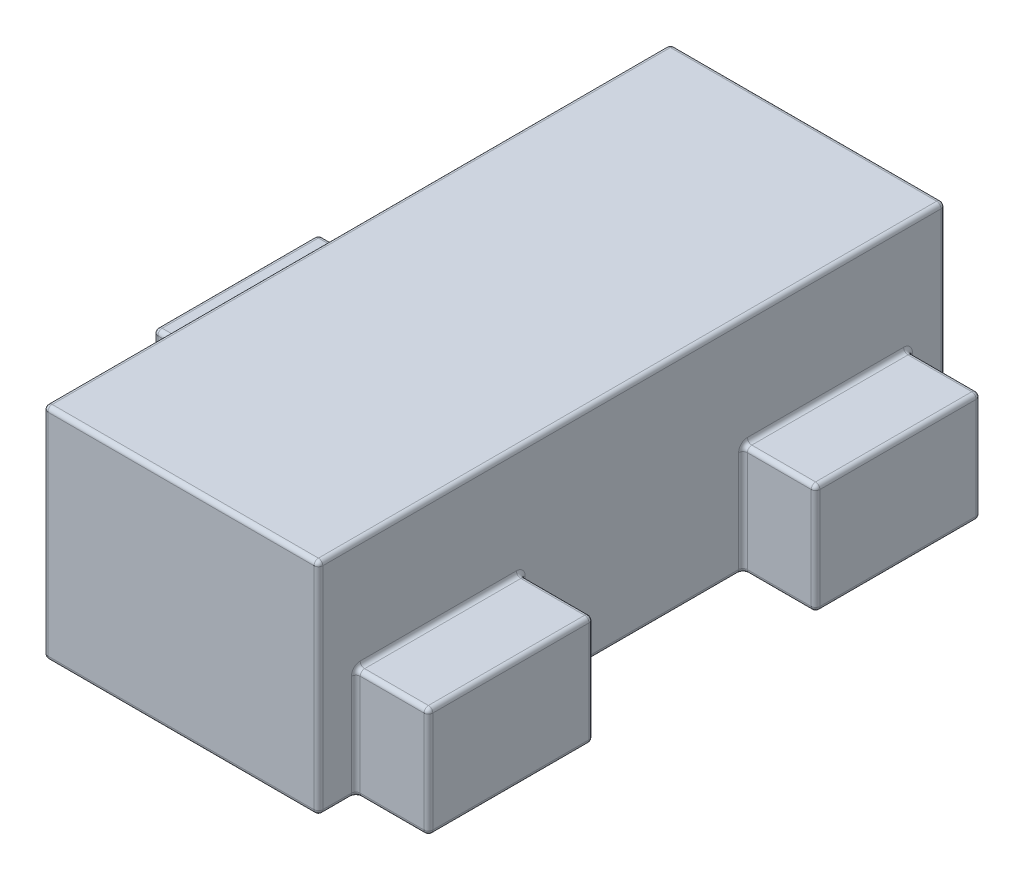
SolidWorks part; units mm, degrees
ref_plane "Front Plane" through (0, 0, 0) normal (0, 0, 1) x (1, 0, 0)
ref_plane "Top Plane" through (0, 0, 0) normal (0, 1, 0) x (1, 0, 0)
ref_plane "Right Plane" through (0, 0, 0) normal (1, 0, 0) x (0, 0, -1)
sketch "Sketch1" plane through (0, 0, 0) normal (0, 1, 0) x (1, 0, 0)
  line L1 (-0.625, 1.425) -> (0.625, 1.425)
  line L2 (-0.625, 1.425) -> (-0.625, -1.425)
  line L3 (-0.625, -1.425) -> (0.625, -1.425)
  line L4 (0.625, 1.425) -> (0.625, -1.425)
  line L5 (-0.625, 1.425) -> (0.625, -1.425) construction
  line L6 (-0.625, -1.425) -> (0.625, 1.425) construction
  point P0 (0, 0)
  dimension "D1" = 1.25
  dimension "D2" = 2.85
extrude "Boss-Extrude1" add sketch "Sketch1" along normal blind 1
sketch "Sketch2" plane through (0, 0, 0) normal (0, 1, 0) x (1, 0, 0)
  line L0 (0, 0) -> (-0.625, 0) construction
  line L1 (-0.625, 1.425) -> (-0.625, -1.425) construction
  line L2 (-0.625, -0.375) -> (-0.625, 0.375)
  line L3 (-0.625, 0.375) -> (-1.175, 0.375)
  line L4 (-1.175, 0.375) -> (-1.175, -0.375)
  line L5 (-1.175, -0.375) -> (-0.625, -0.375)
  line L6 (0.625, -1.425) -> (0.625, 1.425) construction
  line L7 (0.625, 0.505) -> (0.955, 0.505)
  line L8 (0.625, 0.505) -> (0.625, 1.255)
  line L9 (0.625, 1.255) -> (0.955, 1.255)
  line L10 (0.955, 0.505) -> (0.955, 1.255)
  line L11 (0.625, 0.505) -> (0.955, 1.255) construction
  line L12 (0.625, 1.255) -> (0.955, 0.505) construction
  line L13 (0.625, -1.255) -> (0.955, -0.505) construction
  line L14 (0.625, -0.505) -> (0.955, -1.255) construction
  line L15 (0.955, -0.505) -> (0.955, -1.255)
  line L16 (0.625, -1.255) -> (0.955, -1.255)
  line L17 (0.625, -0.505) -> (0.625, -1.255)
  line L18 (0.625, -0.505) -> (0.955, -0.505)
  point P8 (-0.625, 0)
  point P14 (0.79, 0.88)
  point P21 (0.79, -0.88)
  dimension "D1" = 0.75
  dimension "D2" = 0.55
  dimension "D3" = 0.75
  dimension "D4" = 0.33
  dimension "D5" = 0.88
extrude "Boss-Extrude2" add sketch "Sketch2" along normal blind 0.5
fillet "Fillet1" radius 0.02 48 edges at (-0.625, 0.25, 0.375) (-0.625, 0.25, -0.375) (-1.175, 0.25, -0.375) (-1.175, 0.25, 0.375) (0, 1, 1.425) (-0.625, 1, 0) (0.79, 0, 0.505) (0.79, 0.5, 0.505) (0.79, 0, -1.255) (0.79, 0.5, -1.255) (-0.625, 0, -0.9) (-0.9, 0, -0.375) (-0.9, 0.5, -0.375) (-1.175, 0, 0) (-1.175, 0.5, 0) (-0.9, 0, 0.375) (-0.9, 0.5, 0.375) (-0.625, 0, 0.9) (0, 0, 1.425) (0.625, 0, 1.34) (0.625, 0.5, 1.425) (0.625, 1, 0) (0.625, 0, -1.34) (0.625, 0.25, -1.255) (0.625, 0, 0) (0.625, 0.25, 0.505) (-0.625, 0.5, 0) (0.625, 0.5, -1.425) (0, 1, -1.425) (-0.625, 0.5, -1.425) (0, 0, -1.425) (0.625, 0.5, -0.88) (0.625, 0.5, 0.88) (0.625, 0.25, -0.505) (0.79, 0.5, -0.505) (0.79, 0, -0.505) (0.955, 0.25, -0.505) (0.955, 0.5, -0.88) (0.955, 0.25, -1.255) (0.955, 0, -0.88) (0.625, 0.25, 1.255) (0.79, 0.5, 1.255) (0.79, 0, 1.255) (0.955, 0.25, 1.255) (0.955, 0.5, 0.88) (0.955, 0.25, 0.505) (0.955, 0, 0.88) (-0.625, 0.5, 1.425)
sketch "Sketch3" plane through (0, 0, 0) normal (0, -1, 0) x (1, 0, 0)
  line L0 (0.645, 1.235) -> (0.645, 0.525)
  line L1 (0.645, -0.525) -> (0.645, -1.235)
  line L2 (-0.645, 0.355) -> (-0.645, -0.355)
split line "Split Line1"
